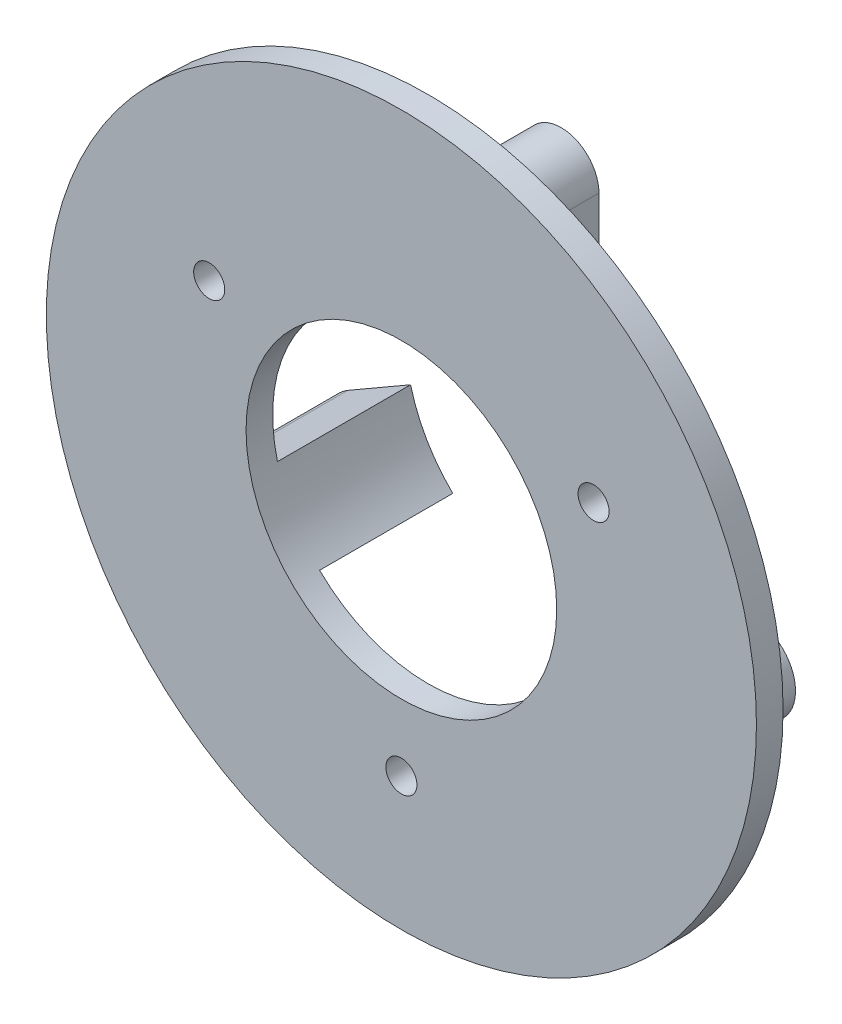
SolidWorks part; units mm, degrees
ref_plane "前视基准面" through (0, 0, 0) normal (0, 0, 1) x (1, 0, 0)
ref_plane "上视基准面" through (0, 0, 0) normal (0, 1, 0) x (1, 0, 0)
ref_plane "右视基准面" through (0, 0, 0) normal (1, 0, 0) x (0, 0, -1)
sketch "草图1" plane through (0, 0, 0) normal (0, 0, 1) x (1, 0, 0)
  circle A0 centre (0, 0) radius 16
extrude "凸台-拉伸1" add sketch "草图1" along normal blind 1.2
sketch "草图2" plane through (0, 0, 1.2) normal (0, 0, 1) x (1, 0, 0)
  circle A0 centre (0, 0) radius 7
extrude "切除-拉伸1" cut sketch "草图2" against normal blind 1.2
sketch "草图3" plane through (0, 0, 1.2) normal (0, 0, 1) x (1, 0, 0)
  circle A2 centre (8.6603, 5) radius 0.7
  circle A3 centre (0, -10) radius 0.7
  circle A4 centre (-8.6603, 5) radius 0.7
extrude "切除-拉伸2" cut sketch "草图3" against normal blind 1.2
sketch "草图4" plane through (0, 0, 0) normal (0, 0, -1) x (-1, 0, 0)
  line L3 (1.7039, 10) -> (1.7039, 5.3952)
  line L16 (-5.5379, -1.0034) -> (-3.6379, -4.2943)
  line L17 (3.6379, -4.2943) -> (5.5379, -1.0034)
  line L18 (1.7039, 5.3952) -> (-1.7039, 5.3952)
  line L19 (-5.5379, -1.0034) -> (-9.6103, -3.3546)
  line L21 (3.6379, -4.2943) -> (7.7103, -6.6454)
  line L25 (-3.6379, -4.2943) -> (-7.7103, -6.6454)
  line L31 (5.5379, -1.0034) -> (9.6103, -3.3546)
  line L32 (-1.7039, 5.3952) -> (-1.7039, 10)
  circle A1 centre (8.6603, -5) radius 0.9
  circle A2 centre (-8.6603, -5) radius 0.9
  circle A3 centre (0, 10) radius 0.9
  arc A4 (1.7039, 10) -> (-1.7039, 10) centre (0, 10) ccw
  arc A5 (7.7103, -6.6454) -> (9.6103, -3.3546) centre (8.6603, -5) ccw
  arc A6 (-9.6103, -3.3546) -> (-7.7103, -6.6454) centre (-8.6603, -5) ccw
extrude "凸台-拉伸2" add sketch "草图4" along normal blind 6
sketch "草图5" plane through (0, 0, 1.2) normal (0, 0, 1) x (1, 0, 0)
  circle A0 centre (0, 0) radius 7
extrude "切除-拉伸3" cut sketch "草图5" against normal blind 11
